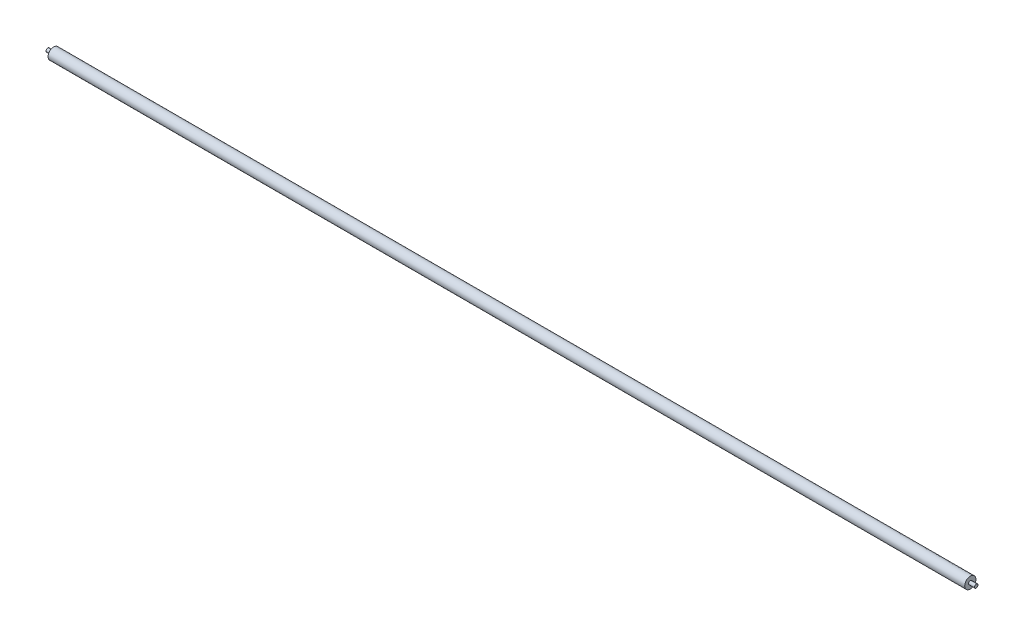
SolidWorks part; units mm, degrees
ref_plane "Front Plane" through (0, 0, 0) normal (0, 0, 1) x (1, 0, 0)
ref_plane "Top Plane" through (0, 0, 0) normal (0, 1, 0) x (1, 0, 0)
ref_plane "Right Plane" through (0, 0, 0) normal (1, 0, 0) x (0, 0, -1)
sketch "Sketch1" plane through (0, 0, 0) normal (1, 0, 0) x (0, 0, -1)
  circle A0 centre (0, 0) radius 9.5
extrude "Boss-Extrude1" add sketch "Sketch1" along normal blind 1554
sketch "Sketch2" plane through (0, 0, 0) normal (-1, 0, 0) x (0, 0, 1)
  circle A0 centre (0, 0) radius 3
extrude "Boss-Extrude2" add sketch "Sketch2" along normal blind 10
sketch "Sketch3" plane through (1554, 0, 0) normal (1, 0, 0) x (0, 0, -1)
  circle A0 centre (0, 0) radius 3
extrude "Boss-Extrude3" add sketch "Sketch3" along normal blind 10
